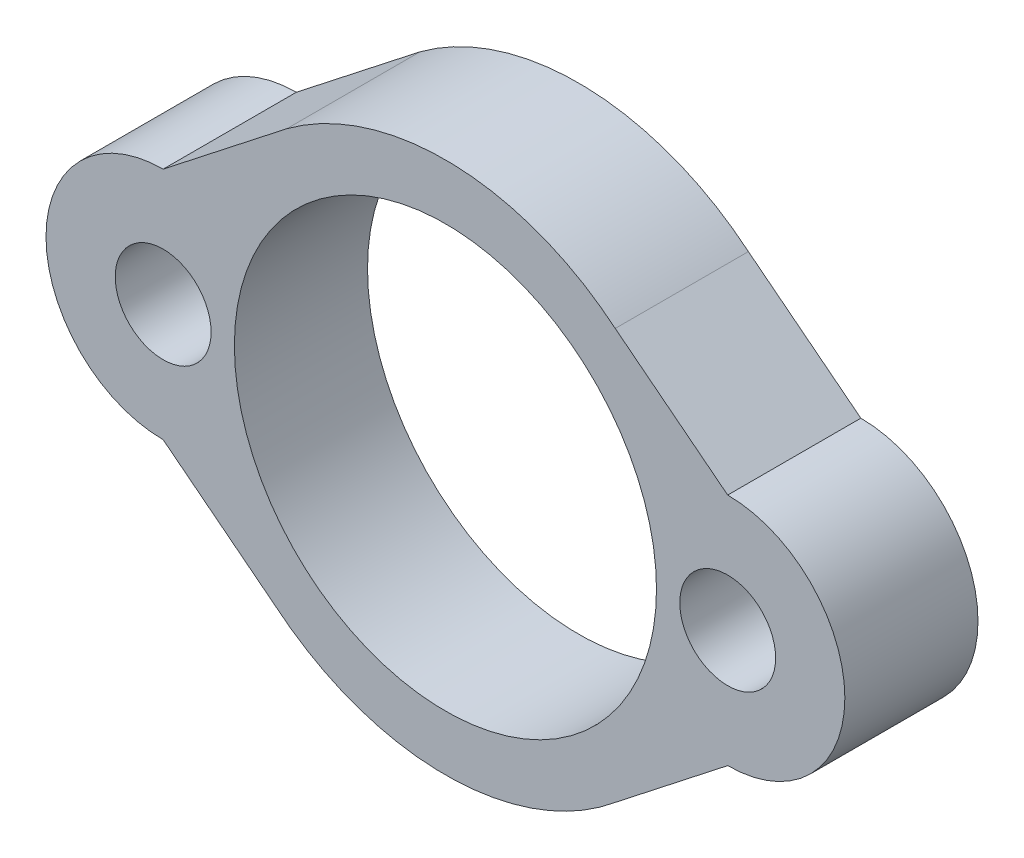
SolidWorks part; units mm, degrees
ref_plane "Front Plane" through (0, 0, 0) normal (0, 0, 1) x (1, 0, 0)
ref_plane "Top Plane" through (0, 0, 0) normal (0, 1, 0) x (1, 0, 0)
ref_plane "Right Plane" through (0, 0, 0) normal (1, 0, 0) x (0, 0, -1)
sketch "Sketch1" plane through (0, 0, 0) normal (0, 0, 1) x (1, 0, 0)
  line L0 (-8.3681, 2.7656) -> (-8.3681, -9.9344) construction
  line L1 (-8.3681, -9.9344) -> (10.6819, -9.9344) construction
  line L2 (10.6819, -9.9344) -> (10.6819, 2.7656) construction
  line L3 (10.6819, 2.7656) -> (-8.3681, 2.7656) construction
  line L4 (-8.3681, -3.5844) -> (10.6819, -3.5844) construction
  line L5 (-5.5741, -0.7904) -> (-2.5309, 1.593)
  line L6 (-5.5741, -6.3784) -> (-2.6418, -8.675)
  line L7 (7.8879, -0.7904) -> (5.2066, 1.3097)
  line L8 (7.8879, -6.3784) -> (5.1904, -8.4912)
  circle A0 centre (1.1569, -3.5844) radius 5.033
  circle A1 centre (-5.5741, -3.5844) radius 1.143
  circle A2 centre (7.8879, -3.5844) radius 1.143
  arc A3 (-2.7585, -8.5836) -> (1.1569, -9.9344) centre (1.1569, -3.5844) ccw
  arc A4 (-5.5741, -0.7904) -> (-5.5741, -6.3784) centre (-5.5741, -3.5844) ccw
  arc A5 (7.8879, -6.3784) -> (7.8879, -0.7904) centre (7.8879, -3.5844) ccw
  arc A6 (1.1569, 2.7656) -> (-2.7585, 1.4148) centre (1.1569, -3.5844) ccw
  arc A7 (7.4228, -2.5403) -> (-5.1089, -2.5403) centre (1.1569, -3.5844) ccw
  arc A8 (-5.1089, -4.6285) -> (7.4228, -4.6285) centre (1.1569, -3.5844) ccw
  dimension "D5" = 2.286
  dimension "D6" = 2.286
  dimension "D7" = 13.462
  dimension "D8" = 2.794
  dimension "D9" = 12.7
  dimension "D1" = 19.05
  dimension "D2" = 12.7
extrude "Boss-Extrude1" add sketch "Sketch1" along normal blind 3.175
